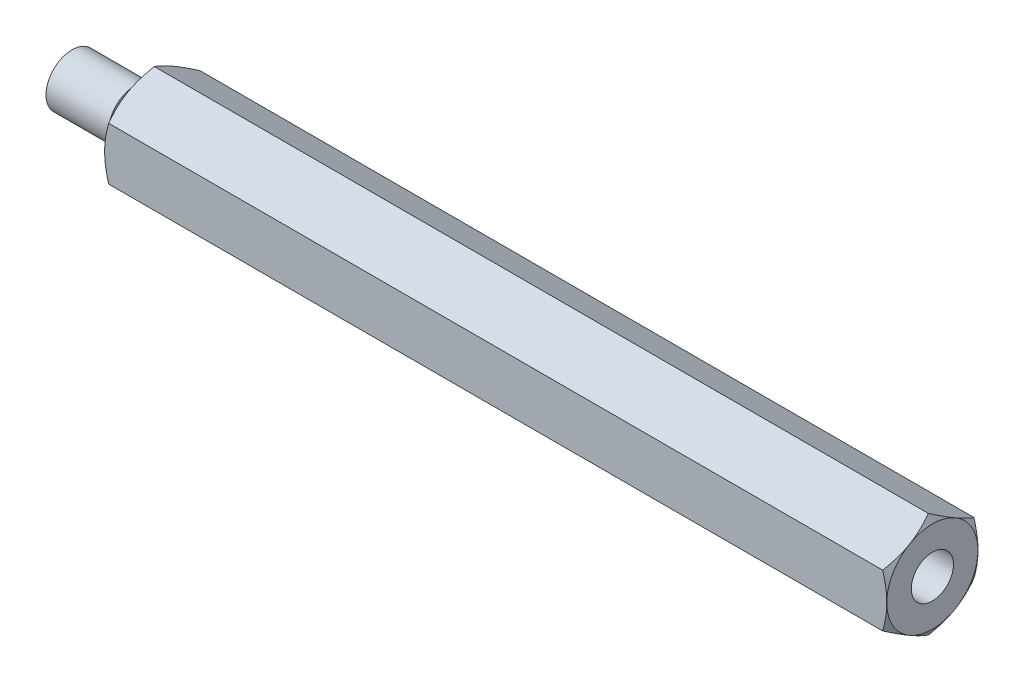
SolidWorks part; units mm, degrees
material "ﾎﾟﾘｵｷｼﾒﾁﾚﾝ(POM)ｱｾﾀｰﾙ共重合体"
ref_plane "Front Plane" through (0, 0, 0) normal (0, 0, 1) x (1, 0, 0)
ref_plane "Top Plane" through (0, 0, 0) normal (0, 1, 0) x (1, 0, 0)
ref_plane "Right Plane" through (0, 0, 0) normal (1, 0, 0) x (0, 0, -1)
sketch "Sketch1" plane through (0, 0, 0) normal (1, 0, 0) x (0, 0, -1)
  line L1 (0, 4.0415) -> (-3.5, 2.0207)
  line L2 (-3.5, 2.0207) -> (-3.5, -2.0207)
  line L3 (-3.5, -2.0207) -> (0, -4.0415)
  line L4 (0, -4.0415) -> (3.5, -2.0207)
  line L5 (3.5, -2.0207) -> (3.5, 2.0207)
  line L6 (3.5, 2.0207) -> (0, 4.0415)
  circle A0 centre (0, 0) radius 3.5 construction
  dimension "C" = 8.0829
  dimension "B" = 7
extrude "Boss-Extrude1" add sketch "Sketch1" along normal blind 60
sketch "Sketch2" plane through (0, 0, 0) normal (0, 0, 1) x (1, 0, 0)
  line L0 (0, 0) -> (60, 0) construction
  line L1 (60, 2.0207) -> (60, -2.0207) construction
  line L2 (0, 4.0415) -> (0, 3.5)
  line L3 (0, 3.5) -> (0.3126, 4.0415)
  line L4 (0.3126, 4.0415) -> (0, 4.0415)
  line L5 (59.6874, 4.0415) -> (60, 4.0415)
  line L6 (60, 4.0415) -> (60, 3.5)
  line L7 (60, 3.5) -> (59.6874, 4.0415)
  line L8 (60, 4.0415) -> (0, 4.0415) construction
  line L9 (0, 4.0415) -> (0, 2.0207) construction
  line L10 (60, 4.0415) -> (60, 2.0207) construction
  dimension "FIX_1" = 30
revolve "Cut-Revolve1" cut sketch "Sketch2" angle 360 about L0
sketch "Sketch3" [suppressed] plane through (0, 0, 0) normal (0, 0, 1) x (1, 0, 0)
  line L0 (0, 0) -> (-4.5, 0) construction
  line L1 (0, 0) -> (0, 1.15)
  line L2 (0, 1.15) -> (-1, 1.15)
  line L3 (-1, 1.15) -> (-1, 1.5)
  line L4 (-1, 1.5) -> (-4.5, 1.5)
  line L5 (-4.5, 1.5) -> (-4.5, 0)
  line L6 (-4.5, 0) -> (0, 0)
  dimension "G_s" = 1.2
  dimension "MC" = 3.2
  dimension "M" = 4
  dimension "Mx1.5" = 6
revolve "Revolve1" [suppressed] add sketch "Sketch3" angle 360 about L0
cosmetic thread "Thread2" [suppressed]
hole_wizard "Tap1" [suppressed] positions "Sketch5" profile "Sketch4" hole size "M3x0.5" standard "JIS"
sketch "Sketch5" [suppressed] plane through (15, 0, 0) normal (1, 0, 0) x (0, 0, -1)
  point P0 (0, 0)
sketch "Sketch4" [suppressed] plane through (15, 0, 0) normal (0, 1, 0) x (0, 0, -1)
  line L0 (0, 0) -> (0, 8.2388)
  line L1 (0, 8.2388) -> (1.2295, 7.5)
  line L2 (1.2295, 7.5) -> (1.2295, 0)
  line L5 (1.2295, 0) -> (0, 0)
  line L10 (0, 8.2388) -> (-1.2295, 7.5) construction
  line L11 (0, 0) -> (0, 8.2388) construction
  dimension "Drill Angle" = 118
  dimension "HSL_1" = 10.1
cosmetic thread "Thread1" [suppressed]
ref_plane "Dim_M" through (4, 0, 0) normal (-1, 0, 0) x (0, 0, 1)
sketch "Sketch6" plane through (0, 0, 0) normal (0, 0, 1) x (1, 0, 0)
  line L0 (0, 0) -> (-6, 0) construction
  line L1 (0, 0) -> (0, 1.6)
  line L2 (0, 1.6) -> (-1.2, 1.6)
  line L3 (-1.2, 1.6) -> (-1.2, 2)
  line L4 (-1.2, 2) -> (-6, 2)
  line L5 (-6, 2) -> (-6, 0)
  line L6 (-6, 0) -> (0, 0)
  line L7 (0, 4.0415) -> (0, 3.5) construction
  dimension "G_s" = 1.2
  dimension "MC" = 3.2
  dimension "M" = 4
  dimension "Mx1.5" = 6
revolve "Revolve2" add sketch "Sketch6" angle 360 about L0
cosmetic thread "Thread3"
hole_wizard "Tap2" positions "Sketch8" profile "Sketch7" hole size "M3x0.5" standard "JIS"
sketch "Sketch8" plane through (60, 0, 0) normal (1, 0, 0) x (0, 0, -1)
  point P0 (0, 0)
sketch "Sketch7" plane through (60, 0, 0) normal (0, 1, 0) x (0, 0, -1)
  line L0 (0, 0) -> (0, 11.074)
  line L1 (0, 11.074) -> (1.621, 10.1)
  line L2 (1.621, 10.1) -> (1.621, 0)
  line L5 (1.621, 0) -> (0, 0)
  line L10 (0, 11.074) -> (-1.621, 10.1) construction
  line L11 (0, 0) -> (0, 11.074) construction
  dimension "Drill Angle" = 118
  dimension "HSL_2" = 10.1
cosmetic thread "Thread4"
hole_wizard "Tap3" [suppressed] positions "Sketch10" profile "Sketch9" hole size "M2.5x0.45" standard "JIS"
sketch "Sketch10" plane through (60, 0, 0) normal (1, 0, 0) x (0, 0, -1)
  point P0 (0, 0)
sketch "Sketch9" plane through (60, 0, 0) normal (0, 1, 0) x (0, 0, -1)
  line L0 (0, 0) -> (0, 9.074)
  line L1 (0, 9.074) -> (1.621, 8.1)
  line L2 (1.621, 8.1) -> (1.621, 0)
  line L5 (1.621, 0) -> (0, 0)
  line L10 (0, 9.074) -> (-1.621, 8.1) construction
  line L11 (0, 0) -> (0, 9.074) construction
  dimension "Drill Angle" = 118
  dimension "HSL_3" = 8.1
cosmetic thread "Thread5" [suppressed]
sketch "Sketch11" [suppressed] plane through (0, 0, 0) normal (0, 0, 1) x (1, 0, 0)
  line L0 (0, 0) -> (-6, 0) construction
  line L1 (0, 0) -> (0, 1.6)
  line L2 (0, 1.6) -> (-1.2, 1.6)
  line L3 (-1.2, 1.6) -> (-1.2, 2)
  line L4 (-1.2, 2) -> (-6, 2)
  line L5 (-6, 2) -> (-6, 0)
  line L6 (-6, 0) -> (0, 0)
  line L8 (0, 4.0415) -> (0, 3.5) construction
  dimension "G_s" = 1.2
  dimension "MC" = 3.2
  dimension "M" = 4
  dimension "Mx1.5" = 6
revolve "Revolve3" [suppressed] add sketch "Sketch11" angle 360 about L0
cosmetic thread "Thread6" [suppressed]
hole_wizard "Tap4" [suppressed] positions "Sketch13" profile "Sketch12" hole size "M3x0.5" standard "JIS"
sketch "Sketch13" [suppressed] plane through (60, 0, 0) normal (1, 0, 0) x (0, 0, -1)
  point P0 (0, 0)
sketch "Sketch12" [suppressed] plane through (60, 0, 0) normal (0, 1, 0) x (0, 0, -1)
  line L0 (0, 0) -> (0, 8.2388)
  line L1 (0, 8.2388) -> (1.2295, 7.5)
  line L2 (1.2295, 7.5) -> (1.2295, 0)
  line L5 (1.2295, 0) -> (0, 0)
  line L10 (0, 8.2388) -> (-1.2295, 7.5) construction
  line L11 (0, 0) -> (0, 8.2388) construction
  dimension "Drill Angle" = 118
  dimension "HSL_4" = 7.5
cosmetic thread "Thread7" [suppressed]
hole_wizard "Tap5" [suppressed] positions "Sketch15" profile "Sketch14" hole size "M2.5x0.45" standard "JIS"
sketch "Sketch15" [suppressed] plane through (15, 0, 0) normal (1, 0, 0) x (0, 0, -1)
  point P0 (0, 0)
sketch "Sketch14" [suppressed] plane through (15, 0, 0) normal (0, 1, 0) x (0, 0, -1)
  line L0 (0, 0) -> (0, 6.7388)
  line L1 (0, 6.7388) -> (1.2295, 6)
  line L2 (1.2295, 6) -> (1.2295, 0)
  line L5 (1.2295, 0) -> (0, 0)
  line L10 (0, 6.7388) -> (-1.2295, 6) construction
  line L11 (0, -6.35) -> (0, 107.95) construction
  dimension "Drill Angle" = 118
  dimension "HSL_5" = 6
cosmetic thread "Thread8" [suppressed]
ref_plane "Dim_N" through (3, 0, 0) normal (-1, 0, 0) x (0, 0, 1)
sketch "Sketch16" [suppressed] plane through (0, 0, 0) normal (0, 0, 1) x (1, 0, 0)
  line L0 (-4.5, 0) -> (15, 0) construction
  line L1 (15, 3.4641) -> (15, 3) construction
  line L4 (-4.5, 0) -> (-4.5, 1.5) construction
  line L7 (-4.5, 0) -> (0, 0)
  line L8 (-4.5, 0) -> (-4.5, 1.5)
  line L9 (-4.5, 1.5) -> (0, 1.5)
  line L10 (0, 0) -> (0, 1.5)
  dimension "M" = 4
  dimension "Mx1.5" = 6
revolve "Cut-Revolve2" [suppressed] cut sketch "Sketch16" angle 360 about L0
sketch "Sketch17" [suppressed] plane through (0, 0, 0) normal (0, 0, 1) x (1, 0, 0)
  line L0 (0, 0) -> (-3, 0) construction
  line L1 (0, 0) -> (0, 1.15)
  line L2 (0, 1.15) -> (-1, 1.15)
  line L3 (-1, 1.15) -> (-1, 1.5)
  line L4 (-1, 1.5) -> (-3, 1.5)
  line L5 (-3, 1.5) -> (-3, 0)
  line L6 (-3, 0) -> (0, 0)
  dimension "G_s" = 1.2
  dimension "MC" = 3.2
  dimension "MLC" = 3
  dimension "M" = 4
revolve "Revolve4" [suppressed] add sketch "Sketch17" angle 360 about L0
cosmetic thread "Thread9" [suppressed]
hole_wizard "Tap6" [suppressed] positions "Sketch19" profile "Sketch18" hole size "M3x0.5" standard "JIS"
sketch "Sketch19" [suppressed] plane through (15, 0, 0) normal (1, 0, 0) x (0, 0, -1)
  point P0 (0, 0)
sketch "Sketch18" [suppressed] plane through (15, 0, 0) normal (0, 1, 0) x (0, 0, -1)
  line L0 (0, 0) -> (0, 11.2388)
  line L1 (0, 11.2388) -> (1.2295, 10.5)
  line L2 (1.2295, 10.5) -> (1.2295, 0)
  line L5 (1.2295, 0) -> (0, 0)
  line L10 (0, 11.2388) -> (-1.2295, 10.5) construction
  line L11 (0, 0) -> (0, 11.2388) construction
  dimension "Drill Angle" = 118
  dimension "HSL_6" = 10.5
cosmetic thread "Thread10" [suppressed]
equation "\"Mx2\"= \"M\" * 2"
equation "\"Factor\"= 1.082532"
equation "\"Pitch_M\"= IIF ( \"M\" = 24 , 3 , IIF ( \"M\" = 20 , 2.5 , IIF ( \"M\" = 16 , 2 , IIF ( \"M\" = 12 , 1.75 , IIF ( \"M\" = 10 , 1.5 , IIF ( \"M\" = 8 , 1.25 , IIF ( \"M\" = 6 , 1 , IIF ( \"M\" = 5 , 0.8 , IIF ( \"M\" = 4 , 0.7 , IIF ( \"M\" = 3 , 0.5 , IIF ( \"M\" = 2.6 , 0.45 , 0.4 ) ) ) ) ) ) ) ) ) ) )"
equation "\"HSD_1\"= round ( \"M\" - \"Factor\" * \"Pitch_M\" , 3 )"
equation "\"HSL_1\"= round ( \"Mx2\" + \"Pitch_M\" * 3 , 1 )"
equation "\"ATD_1\"= round ( \"M\" - \"Factor\" * \"Pitch_M\" , 3 )"
equation "\"Mx1.5\"= \"M\" * 1.5"
equation "\"ATD_2\"= round ( \"M\" - \"Factor\" * \"Pitch_M\" , 3 )"
equation "\"HSD_2\"= round ( \"M\" - \"Factor\" * \"Pitch_M\" , 3 )"
equation "\"HSL_2\"= round ( \"Mx2\" + \"Pitch_M\" * 3 , 1 )"
equation "\"HSD_3\"= round ( \"M\" - \"Factor\" * \"Pitch_M\" , 3 )"
equation "\"HSL_3\"= round ( \"Mx1.5\" + \"Pitch_M\" * 3 , 1 )"
equation "\"ATD_3\"= round ( \"M\" - \"Factor\" * \"Pitch_M\" , 3 )"
equation "\"Nx2\"= \"N\" * 2"
equation "\"Pitch_N\"= IIF ( \"N\" = 24 , 3 , IIF ( \"N\" = 20 , 2.5 , IIF ( \"N\" = 16 , 2 , IIF ( \"N\" = 12 , 1.75 , IIF ( \"N\" = 10 , 1.5 , IIF ( \"N\" = 8 , 1.25 , IIF ( \"N\" = 6 , 1 , IIF ( \"N\" = 5 , 0.8 , IIF ( \"N\" = 4 , 0.7 , IIF ( \"N\" = 3 , 0.5 , IIF ( \"N\" = 2.6 , 0.45 , 0.4 ) ) ) ) ) ) ) ) ) ) )"
equation "\"HSD_4\"= round ( \"N\" - \"Factor\" * \"Pitch_N\" , 3 )"
equation "\"HSL_4\"= round ( \"Nx2\" + \"Pitch_N\" * 3 , 1 )"
equation "\"Nx1.5\"= \"N\" * 1.5"
equation "\"HSD_5\"= round ( \"N\" - \"Factor\" * \"Pitch_N\" , 3 )"
equation "\"HSL_5\"= round ( \"Nx1.5\" + \"Pitch_N\" * 3 , 1 )"
equation "\"ATD_4\"= round ( \"M\" - \"Factor\" * \"Pitch_M\" , 3 )"
equation "\"Nx3\"= \"N\" * 3"
equation "\"HSD_6\"= round ( \"N\" - \"Factor\" * \"Pitch_N\" , 3 )"
equation "\"HSL_6\"= round ( \"Nx3\" + \"Pitch_N\" * 3 , 1 )"
